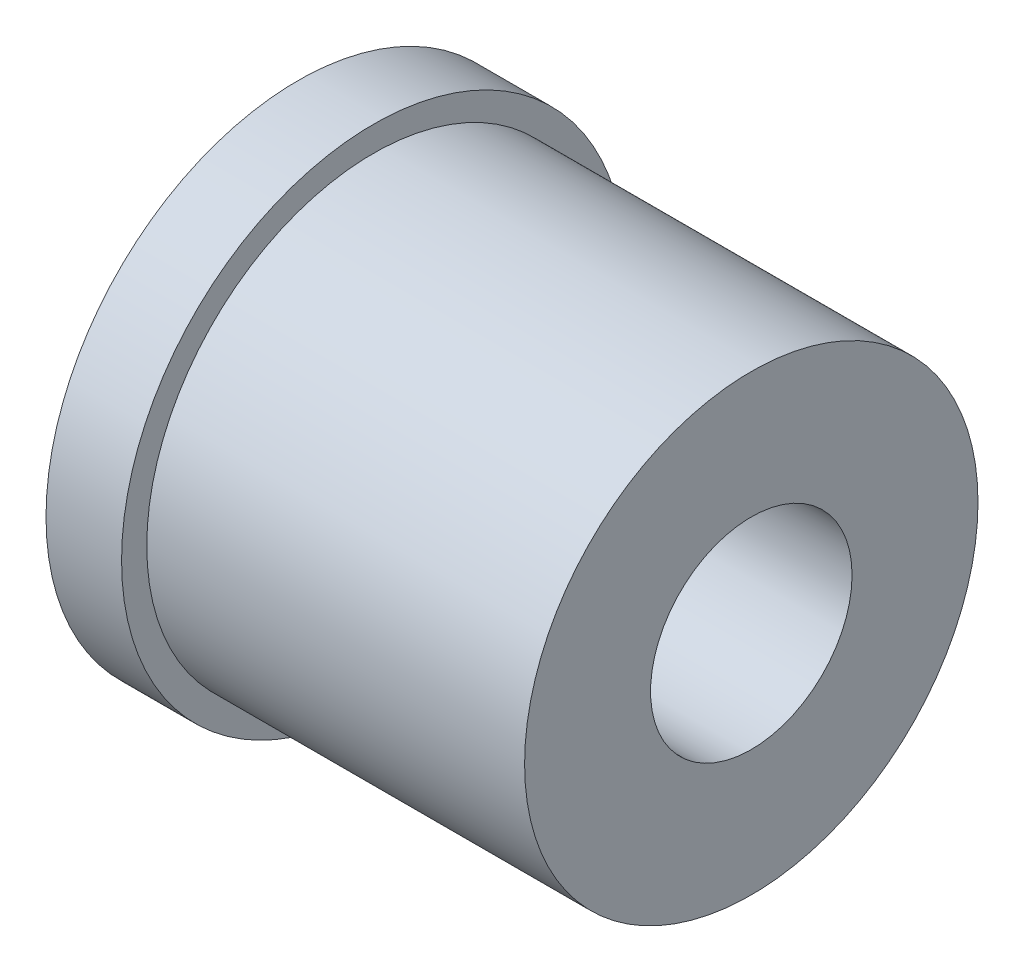
SolidWorks part; units mm, degrees
ref_plane "Front Plane" through (0, 0, 0) normal (0, 0, 1) x (1, 0, 0)
ref_plane "Top Plane" through (0, 0, 0) normal (0, 1, 0) x (1, 0, 0)
ref_plane "Right Plane" through (0, 0, 0) normal (1, 0, 0) x (0, 0, -1)
sketch "Sketch1" plane through (0, 0, 0) normal (1, 0, 0) x (0, 0, -1)
  circle A0 centre (0, 0) radius 2.25
  circle A1 centre (0, 0) radius 1
  dimension "D1" = 2
  dimension "D2" = 4.5
extrude "Boss-Extrude1" add sketch "Sketch1" along normal blind 4.5
sketch "Sketch2" plane through (0, 0, 0) normal (-1, 0, 0) x (0, 0, 1)
  circle A0 centre (0, 0) radius 2.5
  circle A1 centre (0, 0) radius 2.25
  circle A2 centre (0, 0) radius 2.25
  dimension "D2" = 5
  dimension "D1" = 0
extrude "Boss-Extrude2" add sketch "Sketch2" against normal blind 0.75
